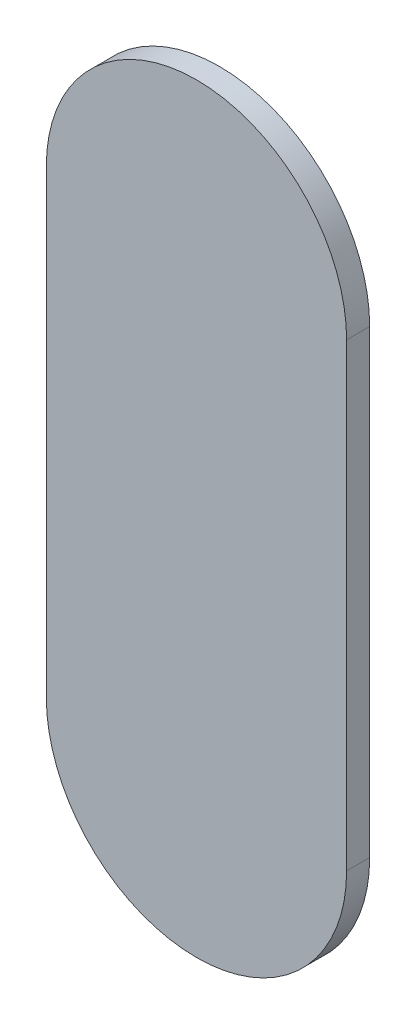
SolidWorks part; units mm, degrees
ref_plane "Front Plane" through (0, 0, 0) normal (0, 0, 1) x (1, 0, 0)
ref_plane "Top Plane" through (0, 0, 0) normal (0, 1, 0) x (1, 0, 0)
ref_plane "Right Plane" through (0, 0, 0) normal (1, 0, 0) x (0, 0, -1)
sketch "Sketch1" plane through (0, 0, 0) normal (0, 0, 1) x (1, 0, 0)
  line L0 (-34.0065, 11.0625) -> (-34.0065, 21.0335) construction
  line L1 (-37.2623, 11.0625) -> (-37.2623, 21.0335)
  line L2 (-30.7506, 11.0625) -> (-30.7506, 21.0335)
  arc A0 (-37.2623, 11.0625) -> (-30.7506, 11.0625) centre (-34.0065, 11.0625) ccw
  arc A1 (-30.7506, 21.0335) -> (-37.2623, 21.0335) centre (-34.0065, 21.0335) ccw
  point P2 (-34.0065, 16.048)
extrude "Boss-Extrude1" add sketch "Sketch1" along normal blind 0.5
